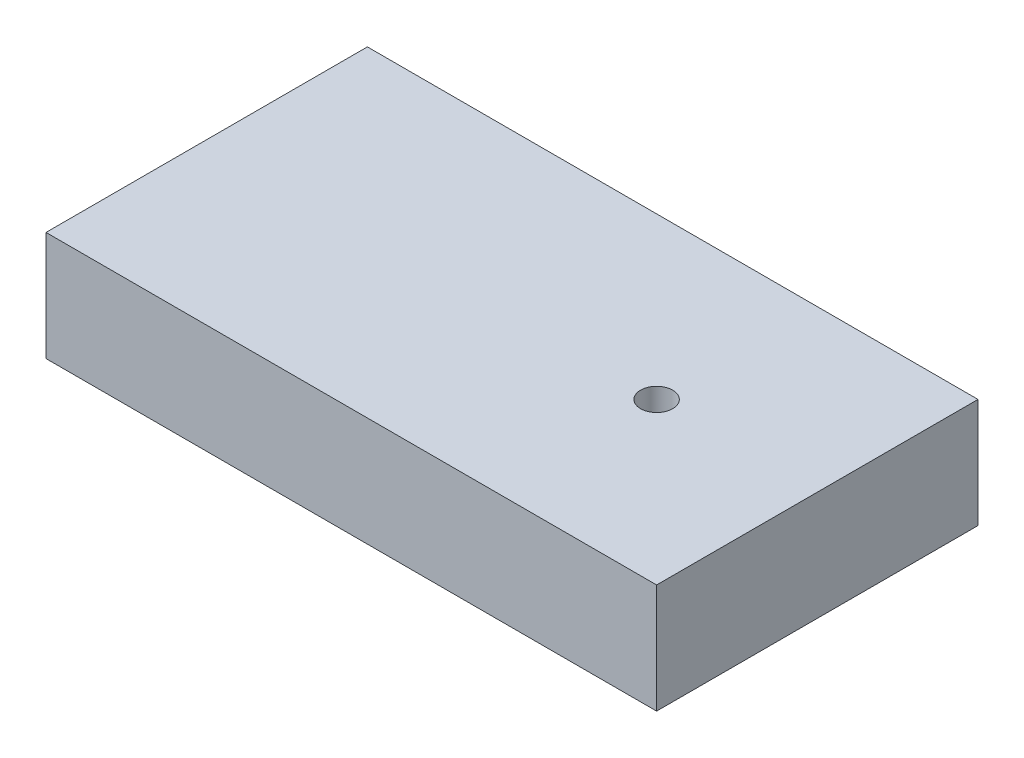
SolidWorks part; units mm, degrees
ref_plane "Front Plane" through (0, 0, 0) normal (0, 0, 1) x (1, 0, 0)
ref_plane "Top Plane" through (0, 0, 0) normal (0, 1, 0) x (1, 0, 0)
ref_plane "Right Plane" through (0, 0, 0) normal (1, 0, 0) x (0, 0, -1)
sketch "Sketch1" plane through (0, 0, 0) normal (0, 1, 0) x (1, 0, 0)
  line L1 (0, 0) -> (48.26, 0)
  line L2 (0, 0) -> (0, 25.4)
  line L3 (0, 25.4) -> (48.26, 25.4)
  line L4 (48.26, 0) -> (48.26, 25.4)
  dimension "D1" = 48.26
  dimension "D2" = 25.4
extrude "Boss-Extrude1" add sketch "Sketch1" along normal blind 8.636
sketch "Sketch2" plane through (0, 8.636, 0) normal (0, 1, 0) x (1, 0, 0)
  line L0 (48.26, 0) -> (48.26, 25.4) construction
  line L1 (48.26, 25.4) -> (0, 25.4) construction
  line L2 (0, 0) -> (48.26, 0) construction
  circle A0 centre (35.56, 12.7) radius 1.27
  dimension "D1" = 2.54
  dimension "D2" = 12.7
  dimension "D3" = 12.7
  dimension "D4" = 12.7
extrude "Cut-Extrude1" cut sketch "Sketch2" against normal through all contours A0
